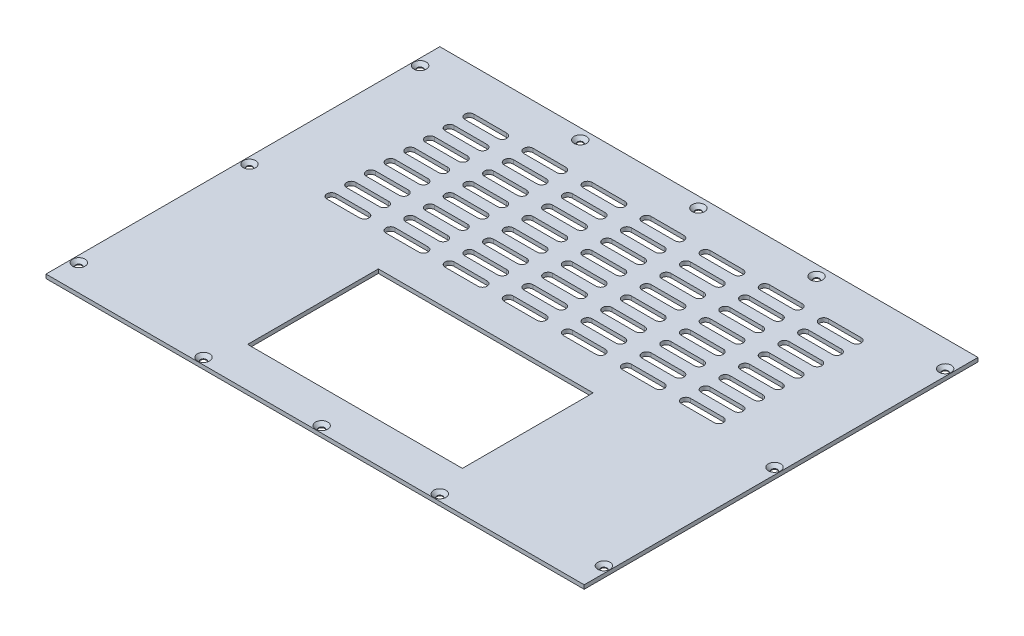
SolidWorks part; units mm, degrees
ref_plane "前基準面" through (0, 0, 0) normal (0, 0, 1) x (1, 0, 0)
ref_plane "上基準面" through (0, 0, 0) normal (0, 1, 0) x (1, 0, 0)
ref_plane "右基準面" through (0, 0, 0) normal (1, 0, 0) x (0, 0, -1)
sketch "草圖1" plane through (0, 0, 0) normal (0, 1, 0) x (1, 0, 0)
  line L1 (-205, -150) -> (205, -150)
  line L2 (-205, -150) -> (-205, 150)
  line L3 (-205, 150) -> (205, 150)
  line L4 (205, -150) -> (205, 150)
  line L5 (-205, -150) -> (205, 150) construction
  line L6 (-205, 150) -> (205, -150) construction
  point P0 (0, 0)
  dimension "D1" = 300
  dimension "D2" = 410
extrude "填料-伸長1" add sketch "草圖1" along normal blind 3
hole_wizard "M4 錐坑平頭螺釘的錐孔1" positions "草圖2" profile "草圖3" countersink size "M4" standard "ISO" end condition through all
sketch "草圖2" plane through (0, 3, 0) normal (0, 1, 0) x (1, 0, 0)
  line L0 (205, 150) -> (-205, 150) construction
  line L1 (-205, 150) -> (-205, -150) construction
  line L2 (-205, -150) -> (205, -150) construction
  line L3 (205, -150) -> (205, 150) construction
  point P0 (0, 142)
  point P2 (-90, 142)
  point P4 (90, 142)
  point P9 (200, 0)
  point P11 (0, -145)
  point P13 (-200, 0)
  point P15 (200, 130)
  point P17 (200, -130)
  point P19 (-200, -130)
  point P21 (-200, 130)
  point P33 (90, -145)
  point P35 (-90, -145)
  dimension "D1" = 8
  dimension "D2" = 90
  dimension "D3" = 90
  dimension "D4" = 130
  dimension "D5" = 130
  dimension "D6" = 5
  dimension "D7" = 130
  dimension "D8" = 130
  dimension "D9" = 5
  dimension "D10" = 5
  dimension "D11" = 150
  dimension "D12" = 150
  dimension "D13" = 205
  dimension "D14" = 205
  dimension "D15" = 90
  dimension "D16" = 90
sketch "草圖3" plane through (0, 3, -142) normal (1, 0, 0) x (0, 0, 1)
  line L0 (0, 0) -> (0, 3)
  line L1 (0, 3) -> (2.25, 3)
  line L2 (2.25, 3) -> (2.25, 2.45)
  line L3 (2.25, 2.45) -> (4.7, 0)
  line L5 (4.7, 0) -> (0, 0)
  line L6 (-2.25, 2.45) -> (-4.7, 0) construction
  line L11 (0, -6.35) -> (0, 107.95) construction
  dimension "貫穿孔直徑" = 4.5
  dimension "貫穿孔深度" = 3
  dimension "近端錐孔直徑" = 9.4
  dimension "近端錐孔角度" = 90
sketch "草圖12" plane through (0, 0, 0) normal (0, -1, 0) x (1, 0, 0)
  line L0 (205, -150) -> (-205, -150) construction
  line L1 (-81.8, 119.6) -> (81.8, 119.6)
  line L2 (-81.8, 119.6) -> (-81.8, 20)
  line L3 (-81.8, 20) -> (81.8, 20)
  line L4 (81.8, 119.6) -> (81.8, 20)
  line L5 (205, 150) -> (205, -150) construction
  point P10 (0, 20)
  dimension "D1" = 170
  dimension "D2" = 205
  dimension "D3" = 163.6
  dimension "D4" = 99.6
extrude "除料-伸長1" cut sketch "草圖12" against normal through all
sketch "草圖13" plane through (0, 3, 0) normal (0, 1, 0) x (1, 0, 0)
  line L0 (-147.5, 115) -> (-122.5, 115) construction
  line L1 (-147.5, 118.5) -> (-122.5, 118.5)
  line L2 (-147.5, 111.5) -> (-122.5, 111.5)
  line L3 (-102.5, 115) -> (-77.5, 115) construction
  line L4 (-102.5, 118.5) -> (-77.5, 118.5)
  line L5 (-102.5, 111.5) -> (-77.5, 111.5)
  line L6 (-57.5, 115) -> (-32.5, 115) construction
  line L7 (-57.5, 118.5) -> (-32.5, 118.5)
  line L8 (-57.5, 111.5) -> (-32.5, 111.5)
  line L9 (-12.5, 115) -> (12.5, 115) construction
  line L10 (-12.5, 118.5) -> (12.5, 118.5)
  line L11 (-12.5, 111.5) -> (12.5, 111.5)
  line L12 (32.5, 115) -> (57.5, 115) construction
  line L13 (32.5, 118.5) -> (57.5, 118.5)
  line L14 (32.5, 111.5) -> (57.5, 111.5)
  line L15 (77.5, 115) -> (102.5, 115) construction
  line L16 (77.5, 118.5) -> (102.5, 118.5)
  line L17 (77.5, 111.5) -> (102.5, 111.5)
  line L18 (122.5, 115) -> (147.5, 115) construction
  line L19 (122.5, 118.5) -> (147.5, 118.5)
  line L20 (122.5, 111.5) -> (147.5, 111.5)
  line L21 (-102.5, 100) -> (-77.5, 100) construction
  line L22 (-102.5, 103.5) -> (-77.5, 103.5)
  line L23 (-102.5, 96.5) -> (-77.5, 96.5)
  line L24 (-57.5, 100) -> (-32.5, 100) construction
  line L25 (-57.5, 103.5) -> (-32.5, 103.5)
  line L26 (-57.5, 96.5) -> (-32.5, 96.5)
  line L27 (-12.5, 100) -> (12.5, 100) construction
  line L28 (-12.5, 103.5) -> (12.5, 103.5)
  line L29 (-12.5, 96.5) -> (12.5, 96.5)
  line L30 (32.5, 100) -> (57.5, 100) construction
  line L31 (32.5, 103.5) -> (57.5, 103.5)
  line L32 (32.5, 96.5) -> (57.5, 96.5)
  line L33 (77.5, 100) -> (102.5, 100) construction
  line L34 (77.5, 103.5) -> (102.5, 103.5)
  line L35 (77.5, 96.5) -> (102.5, 96.5)
  line L36 (122.5, 100) -> (147.5, 100) construction
  line L37 (122.5, 103.5) -> (147.5, 103.5)
  line L38 (122.5, 96.5) -> (147.5, 96.5)
  line L39 (-102.5, 85) -> (-77.5, 85) construction
  line L40 (-102.5, 88.5) -> (-77.5, 88.5)
  line L41 (-102.5, 81.5) -> (-77.5, 81.5)
  line L42 (-57.5, 85) -> (-32.5, 85) construction
  line L43 (-57.5, 88.5) -> (-32.5, 88.5)
  line L44 (-57.5, 81.5) -> (-32.5, 81.5)
  line L45 (-12.5, 85) -> (12.5, 85) construction
  line L46 (-12.5, 88.5) -> (12.5, 88.5)
  line L47 (-12.5, 81.5) -> (12.5, 81.5)
  line L48 (32.5, 85) -> (57.5, 85) construction
  line L49 (32.5, 88.5) -> (57.5, 88.5)
  line L50 (32.5, 81.5) -> (57.5, 81.5)
  line L51 (77.5, 85) -> (102.5, 85) construction
  line L52 (77.5, 88.5) -> (102.5, 88.5)
  line L53 (77.5, 81.5) -> (102.5, 81.5)
  line L54 (122.5, 85) -> (147.5, 85) construction
  line L55 (122.5, 88.5) -> (147.5, 88.5)
  line L56 (122.5, 81.5) -> (147.5, 81.5)
  line L57 (-102.5, 70) -> (-77.5, 70) construction
  line L58 (-102.5, 73.5) -> (-77.5, 73.5)
  line L59 (-102.5, 66.5) -> (-77.5, 66.5)
  line L60 (-57.5, 70) -> (-32.5, 70) construction
  line L61 (-57.5, 73.5) -> (-32.5, 73.5)
  line L62 (-57.5, 66.5) -> (-32.5, 66.5)
  line L63 (-12.5, 70) -> (12.5, 70) construction
  line L64 (-12.5, 73.5) -> (12.5, 73.5)
  line L65 (-12.5, 66.5) -> (12.5, 66.5)
  line L66 (32.5, 70) -> (57.5, 70) construction
  line L67 (32.5, 73.5) -> (57.5, 73.5)
  line L68 (32.5, 66.5) -> (57.5, 66.5)
  line L69 (77.5, 70) -> (102.5, 70) construction
  line L70 (77.5, 73.5) -> (102.5, 73.5)
  line L71 (77.5, 66.5) -> (102.5, 66.5)
  line L72 (122.5, 70) -> (147.5, 70) construction
  line L73 (122.5, 73.5) -> (147.5, 73.5)
  line L74 (122.5, 66.5) -> (147.5, 66.5)
  line L75 (-102.5, 55) -> (-77.5, 55) construction
  line L76 (-102.5, 58.5) -> (-77.5, 58.5)
  line L77 (-102.5, 51.5) -> (-77.5, 51.5)
  line L78 (-57.5, 55) -> (-32.5, 55) construction
  line L79 (-57.5, 58.5) -> (-32.5, 58.5)
  line L80 (-57.5, 51.5) -> (-32.5, 51.5)
  line L81 (-12.5, 55) -> (12.5, 55) construction
  line L82 (-12.5, 58.5) -> (12.5, 58.5)
  line L83 (-12.5, 51.5) -> (12.5, 51.5)
  line L84 (32.5, 55) -> (57.5, 55) construction
  line L85 (32.5, 58.5) -> (57.5, 58.5)
  line L86 (32.5, 51.5) -> (57.5, 51.5)
  line L87 (77.5, 55) -> (102.5, 55) construction
  line L88 (77.5, 58.5) -> (102.5, 58.5)
  line L89 (77.5, 51.5) -> (102.5, 51.5)
  line L90 (122.5, 55) -> (147.5, 55) construction
  line L91 (122.5, 58.5) -> (147.5, 58.5)
  line L92 (122.5, 51.5) -> (147.5, 51.5)
  line L93 (-102.5, 40) -> (-77.5, 40) construction
  line L94 (-102.5, 43.5) -> (-77.5, 43.5)
  line L95 (-102.5, 36.5) -> (-77.5, 36.5)
  line L96 (-57.5, 40) -> (-32.5, 40) construction
  line L97 (-57.5, 43.5) -> (-32.5, 43.5)
  line L98 (-57.5, 36.5) -> (-32.5, 36.5)
  line L99 (-12.5, 40) -> (12.5, 40) construction
  line L100 (-12.5, 43.5) -> (12.5, 43.5)
  line L101 (-12.5, 36.5) -> (12.5, 36.5)
  line L102 (32.5, 40) -> (57.5, 40) construction
  line L103 (32.5, 43.5) -> (57.5, 43.5)
  line L104 (32.5, 36.5) -> (57.5, 36.5)
  line L105 (77.5, 40) -> (102.5, 40) construction
  line L106 (77.5, 43.5) -> (102.5, 43.5)
  line L107 (77.5, 36.5) -> (102.5, 36.5)
  line L108 (122.5, 40) -> (147.5, 40) construction
  line L109 (122.5, 43.5) -> (147.5, 43.5)
  line L110 (122.5, 36.5) -> (147.5, 36.5)
  line L111 (-102.5, 25) -> (-77.5, 25) construction
  line L112 (-102.5, 28.5) -> (-77.5, 28.5)
  line L113 (-102.5, 21.5) -> (-77.5, 21.5)
  line L114 (-57.5, 25) -> (-32.5, 25) construction
  line L115 (-57.5, 28.5) -> (-32.5, 28.5)
  line L116 (-57.5, 21.5) -> (-32.5, 21.5)
  line L117 (-12.5, 25) -> (12.5, 25) construction
  line L118 (-12.5, 28.5) -> (12.5, 28.5)
  line L119 (-12.5, 21.5) -> (12.5, 21.5)
  line L120 (32.5, 25) -> (57.5, 25) construction
  line L121 (32.5, 28.5) -> (57.5, 28.5)
  line L122 (32.5, 21.5) -> (57.5, 21.5)
  line L123 (77.5, 25) -> (102.5, 25) construction
  line L124 (77.5, 28.5) -> (102.5, 28.5)
  line L125 (77.5, 21.5) -> (102.5, 21.5)
  line L126 (122.5, 25) -> (147.5, 25) construction
  line L127 (122.5, 28.5) -> (147.5, 28.5)
  line L128 (122.5, 21.5) -> (147.5, 21.5)
  line L129 (-102.5, 10) -> (-77.5, 10) construction
  line L130 (-102.5, 13.5) -> (-77.5, 13.5)
  line L131 (-102.5, 6.5) -> (-77.5, 6.5)
  line L132 (-57.5, 10) -> (-32.5, 10) construction
  line L133 (-57.5, 13.5) -> (-32.5, 13.5)
  line L134 (-57.5, 6.5) -> (-32.5, 6.5)
  line L135 (-12.5, 10) -> (12.5, 10) construction
  line L136 (-12.5, 13.5) -> (12.5, 13.5)
  line L137 (-12.5, 6.5) -> (12.5, 6.5)
  line L138 (32.5, 10) -> (57.5, 10) construction
  line L139 (32.5, 13.5) -> (57.5, 13.5)
  line L140 (32.5, 6.5) -> (57.5, 6.5)
  line L141 (77.5, 10) -> (102.5, 10) construction
  line L142 (77.5, 13.5) -> (102.5, 13.5)
  line L143 (77.5, 6.5) -> (102.5, 6.5)
  line L144 (122.5, 10) -> (147.5, 10) construction
  line L145 (122.5, 13.5) -> (147.5, 13.5)
  line L146 (122.5, 6.5) -> (147.5, 6.5)
  line L147 (-147.5, 100) -> (-122.5, 100) construction
  line L148 (-147.5, 103.5) -> (-122.5, 103.5)
  line L149 (-147.5, 96.5) -> (-122.5, 96.5)
  line L150 (-147.5, 85) -> (-122.5, 85) construction
  line L151 (-147.5, 88.5) -> (-122.5, 88.5)
  line L152 (-147.5, 81.5) -> (-122.5, 81.5)
  line L153 (-147.5, 70) -> (-122.5, 70) construction
  line L154 (-147.5, 73.5) -> (-122.5, 73.5)
  line L155 (-147.5, 66.5) -> (-122.5, 66.5)
  line L156 (-147.5, 55) -> (-122.5, 55) construction
  line L157 (-147.5, 58.5) -> (-122.5, 58.5)
  line L158 (-147.5, 51.5) -> (-122.5, 51.5)
  line L159 (-147.5, 40) -> (-122.5, 40) construction
  line L160 (-147.5, 43.5) -> (-122.5, 43.5)
  line L161 (-147.5, 36.5) -> (-122.5, 36.5)
  line L162 (-147.5, 25) -> (-122.5, 25) construction
  line L163 (-147.5, 28.5) -> (-122.5, 28.5)
  line L164 (-147.5, 21.5) -> (-122.5, 21.5)
  line L165 (-147.5, 10) -> (-122.5, 10) construction
  line L166 (-147.5, 13.5) -> (-122.5, 13.5)
  line L167 (-147.5, 6.5) -> (-122.5, 6.5)
  line L169 (205, -150) -> (205, 150) construction
  line L171 (205, 150) -> (-205, 150) construction
  arc A0 (-147.5, 118.5) -> (-147.5, 111.5) centre (-147.5, 115) ccw
  arc A1 (-122.5, 111.5) -> (-122.5, 118.5) centre (-122.5, 115) ccw
  arc A2 (-102.5, 118.5) -> (-102.5, 111.5) centre (-102.5, 115) ccw
  arc A3 (-77.5, 111.5) -> (-77.5, 118.5) centre (-77.5, 115) ccw
  arc A4 (-57.5, 118.5) -> (-57.5, 111.5) centre (-57.5, 115) ccw
  arc A5 (-32.5, 111.5) -> (-32.5, 118.5) centre (-32.5, 115) ccw
  arc A6 (-12.5, 118.5) -> (-12.5, 111.5) centre (-12.5, 115) ccw
  arc A7 (12.5, 111.5) -> (12.5, 118.5) centre (12.5, 115) ccw
  arc A8 (32.5, 118.5) -> (32.5, 111.5) centre (32.5, 115) ccw
  arc A9 (57.5, 111.5) -> (57.5, 118.5) centre (57.5, 115) ccw
  arc A10 (77.5, 118.5) -> (77.5, 111.5) centre (77.5, 115) ccw
  arc A11 (102.5, 111.5) -> (102.5, 118.5) centre (102.5, 115) ccw
  arc A12 (122.5, 118.5) -> (122.5, 111.5) centre (122.5, 115) ccw
  arc A13 (147.5, 111.5) -> (147.5, 118.5) centre (147.5, 115) ccw
  arc A14 (-102.5, 103.5) -> (-102.5, 96.5) centre (-102.5, 100) ccw
  arc A15 (-77.5, 96.5) -> (-77.5, 103.5) centre (-77.5, 100) ccw
  arc A16 (-57.5, 103.5) -> (-57.5, 96.5) centre (-57.5, 100) ccw
  arc A17 (-32.5, 96.5) -> (-32.5, 103.5) centre (-32.5, 100) ccw
  arc A18 (-12.5, 103.5) -> (-12.5, 96.5) centre (-12.5, 100) ccw
  arc A19 (12.5, 96.5) -> (12.5, 103.5) centre (12.5, 100) ccw
  arc A20 (32.5, 103.5) -> (32.5, 96.5) centre (32.5, 100) ccw
  arc A21 (57.5, 96.5) -> (57.5, 103.5) centre (57.5, 100) ccw
  arc A22 (77.5, 103.5) -> (77.5, 96.5) centre (77.5, 100) ccw
  arc A23 (102.5, 96.5) -> (102.5, 103.5) centre (102.5, 100) ccw
  arc A24 (122.5, 103.5) -> (122.5, 96.5) centre (122.5, 100) ccw
  arc A25 (147.5, 96.5) -> (147.5, 103.5) centre (147.5, 100) ccw
  arc A26 (-102.5, 88.5) -> (-102.5, 81.5) centre (-102.5, 85) ccw
  arc A27 (-77.5, 81.5) -> (-77.5, 88.5) centre (-77.5, 85) ccw
  arc A28 (-57.5, 88.5) -> (-57.5, 81.5) centre (-57.5, 85) ccw
  arc A29 (-32.5, 81.5) -> (-32.5, 88.5) centre (-32.5, 85) ccw
  arc A30 (-12.5, 88.5) -> (-12.5, 81.5) centre (-12.5, 85) ccw
  arc A31 (12.5, 81.5) -> (12.5, 88.5) centre (12.5, 85) ccw
  arc A32 (32.5, 88.5) -> (32.5, 81.5) centre (32.5, 85) ccw
  arc A33 (57.5, 81.5) -> (57.5, 88.5) centre (57.5, 85) ccw
  arc A34 (77.5, 88.5) -> (77.5, 81.5) centre (77.5, 85) ccw
  arc A35 (102.5, 81.5) -> (102.5, 88.5) centre (102.5, 85) ccw
  arc A36 (122.5, 88.5) -> (122.5, 81.5) centre (122.5, 85) ccw
  arc A37 (147.5, 81.5) -> (147.5, 88.5) centre (147.5, 85) ccw
  arc A38 (-102.5, 73.5) -> (-102.5, 66.5) centre (-102.5, 70) ccw
  arc A39 (-77.5, 66.5) -> (-77.5, 73.5) centre (-77.5, 70) ccw
  arc A40 (-57.5, 73.5) -> (-57.5, 66.5) centre (-57.5, 70) ccw
  arc A41 (-32.5, 66.5) -> (-32.5, 73.5) centre (-32.5, 70) ccw
  arc A42 (-12.5, 73.5) -> (-12.5, 66.5) centre (-12.5, 70) ccw
  arc A43 (12.5, 66.5) -> (12.5, 73.5) centre (12.5, 70) ccw
  arc A44 (32.5, 73.5) -> (32.5, 66.5) centre (32.5, 70) ccw
  arc A45 (57.5, 66.5) -> (57.5, 73.5) centre (57.5, 70) ccw
  arc A46 (77.5, 73.5) -> (77.5, 66.5) centre (77.5, 70) ccw
  arc A47 (102.5, 66.5) -> (102.5, 73.5) centre (102.5, 70) ccw
  arc A48 (122.5, 73.5) -> (122.5, 66.5) centre (122.5, 70) ccw
  arc A49 (147.5, 66.5) -> (147.5, 73.5) centre (147.5, 70) ccw
  arc A50 (-102.5, 58.5) -> (-102.5, 51.5) centre (-102.5, 55) ccw
  arc A51 (-77.5, 51.5) -> (-77.5, 58.5) centre (-77.5, 55) ccw
  arc A52 (-57.5, 58.5) -> (-57.5, 51.5) centre (-57.5, 55) ccw
  arc A53 (-32.5, 51.5) -> (-32.5, 58.5) centre (-32.5, 55) ccw
  arc A54 (-12.5, 58.5) -> (-12.5, 51.5) centre (-12.5, 55) ccw
  arc A55 (12.5, 51.5) -> (12.5, 58.5) centre (12.5, 55) ccw
  arc A56 (32.5, 58.5) -> (32.5, 51.5) centre (32.5, 55) ccw
  arc A57 (57.5, 51.5) -> (57.5, 58.5) centre (57.5, 55) ccw
  arc A58 (77.5, 58.5) -> (77.5, 51.5) centre (77.5, 55) ccw
  arc A59 (102.5, 51.5) -> (102.5, 58.5) centre (102.5, 55) ccw
  arc A60 (122.5, 58.5) -> (122.5, 51.5) centre (122.5, 55) ccw
  arc A61 (147.5, 51.5) -> (147.5, 58.5) centre (147.5, 55) ccw
  arc A62 (-102.5, 43.5) -> (-102.5, 36.5) centre (-102.5, 40) ccw
  arc A63 (-77.5, 36.5) -> (-77.5, 43.5) centre (-77.5, 40) ccw
  arc A64 (-57.5, 43.5) -> (-57.5, 36.5) centre (-57.5, 40) ccw
  arc A65 (-32.5, 36.5) -> (-32.5, 43.5) centre (-32.5, 40) ccw
  arc A66 (-12.5, 43.5) -> (-12.5, 36.5) centre (-12.5, 40) ccw
  arc A67 (12.5, 36.5) -> (12.5, 43.5) centre (12.5, 40) ccw
  arc A68 (32.5, 43.5) -> (32.5, 36.5) centre (32.5, 40) ccw
  arc A69 (57.5, 36.5) -> (57.5, 43.5) centre (57.5, 40) ccw
  arc A70 (77.5, 43.5) -> (77.5, 36.5) centre (77.5, 40) ccw
  arc A71 (102.5, 36.5) -> (102.5, 43.5) centre (102.5, 40) ccw
  arc A72 (122.5, 43.5) -> (122.5, 36.5) centre (122.5, 40) ccw
  arc A73 (147.5, 36.5) -> (147.5, 43.5) centre (147.5, 40) ccw
  arc A74 (-102.5, 28.5) -> (-102.5, 21.5) centre (-102.5, 25) ccw
  arc A75 (-77.5, 21.5) -> (-77.5, 28.5) centre (-77.5, 25) ccw
  arc A76 (-57.5, 28.5) -> (-57.5, 21.5) centre (-57.5, 25) ccw
  arc A77 (-32.5, 21.5) -> (-32.5, 28.5) centre (-32.5, 25) ccw
  arc A78 (-12.5, 28.5) -> (-12.5, 21.5) centre (-12.5, 25) ccw
  arc A79 (12.5, 21.5) -> (12.5, 28.5) centre (12.5, 25) ccw
  arc A80 (32.5, 28.5) -> (32.5, 21.5) centre (32.5, 25) ccw
  arc A81 (57.5, 21.5) -> (57.5, 28.5) centre (57.5, 25) ccw
  arc A82 (77.5, 28.5) -> (77.5, 21.5) centre (77.5, 25) ccw
  arc A83 (102.5, 21.5) -> (102.5, 28.5) centre (102.5, 25) ccw
  arc A84 (122.5, 28.5) -> (122.5, 21.5) centre (122.5, 25) ccw
  arc A85 (147.5, 21.5) -> (147.5, 28.5) centre (147.5, 25) ccw
  arc A86 (-102.5, 13.5) -> (-102.5, 6.5) centre (-102.5, 10) ccw
  arc A87 (-77.5, 6.5) -> (-77.5, 13.5) centre (-77.5, 10) ccw
  arc A88 (-57.5, 13.5) -> (-57.5, 6.5) centre (-57.5, 10) ccw
  arc A89 (-32.5, 6.5) -> (-32.5, 13.5) centre (-32.5, 10) ccw
  arc A90 (-12.5, 13.5) -> (-12.5, 6.5) centre (-12.5, 10) ccw
  arc A91 (12.5, 6.5) -> (12.5, 13.5) centre (12.5, 10) ccw
  arc A92 (32.5, 13.5) -> (32.5, 6.5) centre (32.5, 10) ccw
  arc A93 (57.5, 6.5) -> (57.5, 13.5) centre (57.5, 10) ccw
  arc A94 (77.5, 13.5) -> (77.5, 6.5) centre (77.5, 10) ccw
  arc A95 (102.5, 6.5) -> (102.5, 13.5) centre (102.5, 10) ccw
  arc A96 (122.5, 13.5) -> (122.5, 6.5) centre (122.5, 10) ccw
  arc A97 (147.5, 6.5) -> (147.5, 13.5) centre (147.5, 10) ccw
  arc A98 (-147.5, 103.5) -> (-147.5, 96.5) centre (-147.5, 100) ccw
  arc A99 (-122.5, 96.5) -> (-122.5, 103.5) centre (-122.5, 100) ccw
  arc A100 (-147.5, 88.5) -> (-147.5, 81.5) centre (-147.5, 85) ccw
  arc A101 (-122.5, 81.5) -> (-122.5, 88.5) centre (-122.5, 85) ccw
  arc A102 (-147.5, 73.5) -> (-147.5, 66.5) centre (-147.5, 70) ccw
  arc A103 (-122.5, 66.5) -> (-122.5, 73.5) centre (-122.5, 70) ccw
  arc A104 (-147.5, 58.5) -> (-147.5, 51.5) centre (-147.5, 55) ccw
  arc A105 (-122.5, 51.5) -> (-122.5, 58.5) centre (-122.5, 55) ccw
  arc A106 (-147.5, 43.5) -> (-147.5, 36.5) centre (-147.5, 40) ccw
  arc A107 (-122.5, 36.5) -> (-122.5, 43.5) centre (-122.5, 40) ccw
  arc A108 (-147.5, 28.5) -> (-147.5, 21.5) centre (-147.5, 25) ccw
  arc A109 (-122.5, 21.5) -> (-122.5, 28.5) centre (-122.5, 25) ccw
  arc A110 (-147.5, 13.5) -> (-147.5, 6.5) centre (-147.5, 10) ccw
  arc A111 (-122.5, 6.5) -> (-122.5, 13.5) centre (-122.5, 10) ccw
  point P2 (-135, 115)
  point P11 (-90, 115)
  point P18 (-45, 115)
  point P25 (0, 115)
  point P32 (45, 115)
  point P39 (90, 115)
  point P46 (135, 115)
  point P53 (-90, 100)
  point P60 (-45, 100)
  point P67 (0, 100)
  point P74 (45, 100)
  point P81 (90, 100)
  point P88 (135, 100)
  point P95 (-90, 85)
  point P102 (-45, 85)
  point P109 (0, 85)
  point P116 (45, 85)
  point P123 (90, 85)
  point P130 (135, 85)
  point P137 (-90, 70)
  point P144 (-45, 70)
  point P151 (0, 70)
  point P158 (45, 70)
  point P165 (90, 70)
  point P172 (135, 70)
  point P179 (-90, 55)
  point P186 (-45, 55)
  point P193 (0, 55)
  point P200 (45, 55)
  point P207 (90, 55)
  point P214 (135, 55)
  point P221 (-90, 40)
  point P228 (-45, 40)
  point P235 (0, 40)
  point P242 (45, 40)
  point P249 (90, 40)
  point P256 (135, 40)
  point P263 (-90, 25)
  point P270 (-45, 25)
  point P277 (0, 25)
  point P284 (45, 25)
  point P291 (90, 25)
  point P298 (135, 25)
  point P305 (-90, 10)
  point P312 (-45, 10)
  point P319 (0, 10)
  point P326 (45, 10)
  point P333 (90, 10)
  point P340 (135, 10)
  point P347 (-135, 100)
  point P354 (-135, 85)
  point P361 (-135, 70)
  point P368 (-135, 55)
  point P375 (-135, 40)
  point P382 (-135, 25)
  point P389 (-135, 10)
  dimension "D2" = 3.5
  dimension "D1" = 25
  dimension "D3" = 7
  dimension "D5" = 57.5
  dimension "D6" = 35
  dimension "D4" = 8
extrude "除料-伸長3" cut sketch "草圖13" against normal blind 10
